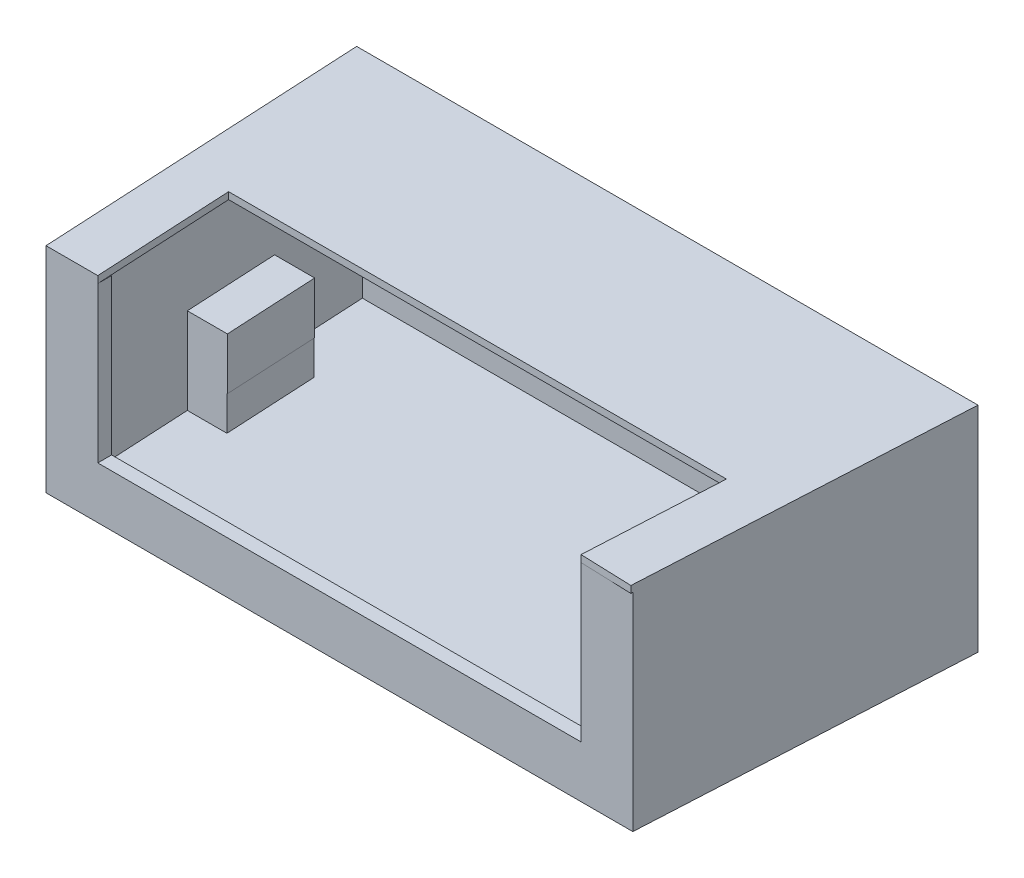
SolidWorks part; units mm, degrees
ref_plane "Спереди" through (0, 0, 0) normal (0, 0, 1) x (1, 0, 0)
ref_plane "Сверху" through (0, 0, 0) normal (0, 1, 0) x (1, 0, 0)
ref_plane "Справа" through (0, 0, 0) normal (1, 0, 0) x (0, 0, -1)
sketch "Эскиз1" plane through (0, 0, 0) normal (0, 1, 0) x (1, 0, 0)
  line L4 (0, 1010.0157) -> (0, -60.2956) construction
  line L5 (-900, 950) -> (900, 950)
  line L6 (900, 950) -> (850, 0)
  line L7 (850, 0) -> (-850, 0)
  line L8 (-900, 950) -> (-850, 0)
  point P2 (0, 143.8504)
  point P4 (0, 0)
  point P8 (0, 0)
  point P10 (0, 0)
  point P11 (0, 950)
  point P12 (0, 0)
  point P13 (0, 0)
  point P14 (0, 0)
  point P15 (0, 0)
  point P16 (0, 0)
  point P17 (0, 0)
  point P18 (0, 1010.0157)
  point P19 (0, 0)
  point P20 (0, 0)
extrude "Бобышка-Вытянуть1" add sketch "Эскиз1" along normal blind 600
sketch "Эскиз3" plane through (0, 600, 0) normal (0, 1, 0) x (1, 0, 0)
  line L0 (-830.0844, 896.6037) -> (830.0844, 896.6037)
  line L1 (830.0844, 896.6037) -> (785, 40)
  line L2 (785, 40) -> (-785, 40)
  line L3 (-785, 40) -> (-830.0844, 896.6037)
  line L4 (-900, 950) -> (-850, 0) construction
  line L5 (850, 0) -> (900, 950) construction
  point P2 (0, 0)
  point P5 (-59.9197, 86.7062)
  point P6 (-58.0427, 86.5619)
  point P7 (-50.1015, 9.4604)
  point P8 (51.1122, 86.7062)
  point P9 (44.0374, 9.4604)
  point P10 (-42.7379, 10.0379)
  point P11 (-52.5561, 86.4175)
  point P12 (58.909, 85.5512)
  point P13 (50.8235, 10.6154)
  point P14 (-51.2566, 10.3267)
  point P15 (-58.6202, 86.4175)
  point P17 (0, 0)
  point P18 (0, 0)
  point P19 (0, 0)
  point P21 (0, 0)
  point P22 (0, 0)
  point P23 (-54.1443, 10.3267)
  point P26 (0, 0)
  point P29 (0, 0)
  point P30 (0, 0)
  point P31 (-742.5505, 896.6037)
  point P32 (-699.6476, 30.2947)
  point P33 (707.8982, 38.5453)
  point P34 (0, 0)
  point P35 (0, 0)
  point P36 (0, 0)
  point P37 (0, 0)
  point P38 (0, 0)
  point P39 (0, 0)
extrude "Вырез-Вытянуть1" cut sketch "Эскиз3" against normal blind 300
sketch "Эскиз4" plane through (0, 300, 0) normal (0, 1, 0) x (1, 0, 0)
  line L0 (-830.0844, 896.6037) -> (830.0844, 896.6037)
  line L1 (830.0844, 896.6037) -> (815.9553, 628.151)
  line L2 (850, 0) -> (900, 950) construction
  line L3 (815.9553, 628.151) -> (709.1357, 628.151)
  line L4 (709.1357, 628.151) -> (695.0962, 361.399)
  line L5 (695.0962, 361.399) -> (801.9157, 361.399)
  line L6 (801.9157, 361.399) -> (785, 40)
  line L7 (785, 40) -> (700, 40)
  line L8 (-785, 40) -> (785, 40) construction
  line L9 (700, 40) -> (700, 0)
  line L10 (700, 0) -> (-700, 0)
  line L11 (-850, 0) -> (850, 0) construction
  line L12 (-700, 0) -> (-700, 40)
  line L13 (-785, 40) -> (785, 40) construction
  line L14 (-700, 40) -> (-785, 40)
  line L15 (-785, 40) -> (-801.9157, 361.399)
  line L17 (-801.9157, 361.399) -> (-685.8143, 361.399)
  line L18 (-685.8143, 361.399) -> (-699.8539, 628.151)
  line L19 (-699.8539, 628.151) -> (-815.9553, 628.151)
  line L21 (-815.9553, 628.151) -> (-830.0844, 896.6037)
  line L22 (-900, 950) -> (-850, 0) construction
  line L23 (-830.0844, 896.6037) -> (-785, 40) construction
  line L24 (785, 40) -> (830.0844, 896.6037) construction
  point P4 (-48.0801, 36.6047)
  point P6 (52, 10)
  point P7 (56.5989, 10)
  point P18 (-700, 0)
  point P24 (740.6941, 628.151)
  point P26 (-741.8804, 832.7188)
  point P32 (-491.7335, 419.7212)
  point P33 (-49.1468, 62.0164)
  point P34 (-52, 10)
  point P35 (-52, 10)
  point P36 (52, 10)
  point P37 (52, 10)
  point P39 (52, 10)
  point P40 (58.2471, 36.6047)
  point P41 (51.8342, 37.0379)
  point P42 (56.077, 10)
  point P45 (-559.3881, 635.8859)
  point P46 (-48.0801, 38.5453)
  point P47 (719.5716, 260.3404)
  point P50 (148.9549, 639.2086)
  point P51 (192.3747, 333.3497)
  point P52 (707.8982, 38.5453)
  point P53 (0, 0)
  point P54 (709.1357, 628.151)
  point P55 (0, 0)
  point P56 (0, 0)
extrude "Вырез-Вытянуть2" cut sketch "Эскиз4" against normal blind 150 and the other way blind 310
sketch "Эскиз5" plane through (0, 150, 0) normal (0, 1, 0) x (1, 0, 0)
  line L0 (-830.0844, 896.6037) -> (-815.9553, 628.151)
  line L1 (830.0844, 896.6037) -> (-830.0844, 896.6037) construction
  line L2 (-830.0844, 896.6037) -> (-815.9553, 628.151) construction
  line L3 (-815.9553, 628.151) -> (-701.3253, 628.151)
  line L4 (-701.3253, 628.151) -> (-687.2857, 361.399)
  line L5 (-687.2857, 361.399) -> (-801.9157, 361.399)
  line L6 (-801.9157, 361.399) -> (-785, 40)
  line L7 (-785, 40) -> (785, 40)
  line L8 (785, 40) -> (801.9157, 361.399)
  line L9 (801.9157, 361.399) -> (694.5809, 361.399)
  line L12 (815.9553, 628.151) -> (830.0844, 896.6037)
  line L13 (830.0844, 896.6037) -> (-830.0844, 896.6037)
  line L16 (785, 40) -> (830.0844, 896.6037) construction
  line L17 (785, 40) -> (801.9157, 361.399) construction
  line L18 (801.9157, 361.399) -> (695.0962, 361.399) construction
  line L19 (801.9157, 361.399) -> (695.0962, 361.399) construction
  line L20 (694.5809, 361.399) -> (708.8148, 628.151)
  line L21 (708.8148, 628.151) -> (815.9553, 628.151)
  line L22 (801.9157, 361.399) -> (815.9553, 628.151) construction
  point P7 (801.9157, 361.399)
extrude "Вырез-Вытянуть3" cut sketch "Эскиз5" against normal blind 100
sketch "Эскиз6" plane through (0, 600, 0) normal (0, 1, 0) x (1, 0, 0)
  line L0 (-900, 950) -> (-850, 0)
  line L1 (-900, 950) -> (-850, 0) construction
  line L3 (850, 0) -> (900, 950) construction
  line L4 (849.7229, -5.2648) -> (900, 950)
  line L5 (900, 950) -> (-900, 950)
  line L6 (-850, 0) -> (-700, 0) construction
  line L7 (-850, 0) -> (-700, 0)
  line L8 (-700, 0) -> (-721.056, 400.064)
  line L9 (-721.056, 400.064) -> (721.056, 400.064)
  line L10 (721.056, 400.064) -> (700, 0)
  line L11 (700, 0) -> (849.7229, -5.2648)
  point P5 (-725.8431, 535.3322)
  point P19 (0, 0)
extrude "Бобышка-Вытянуть2" add sketch "Эскиз6" along normal blind 20
